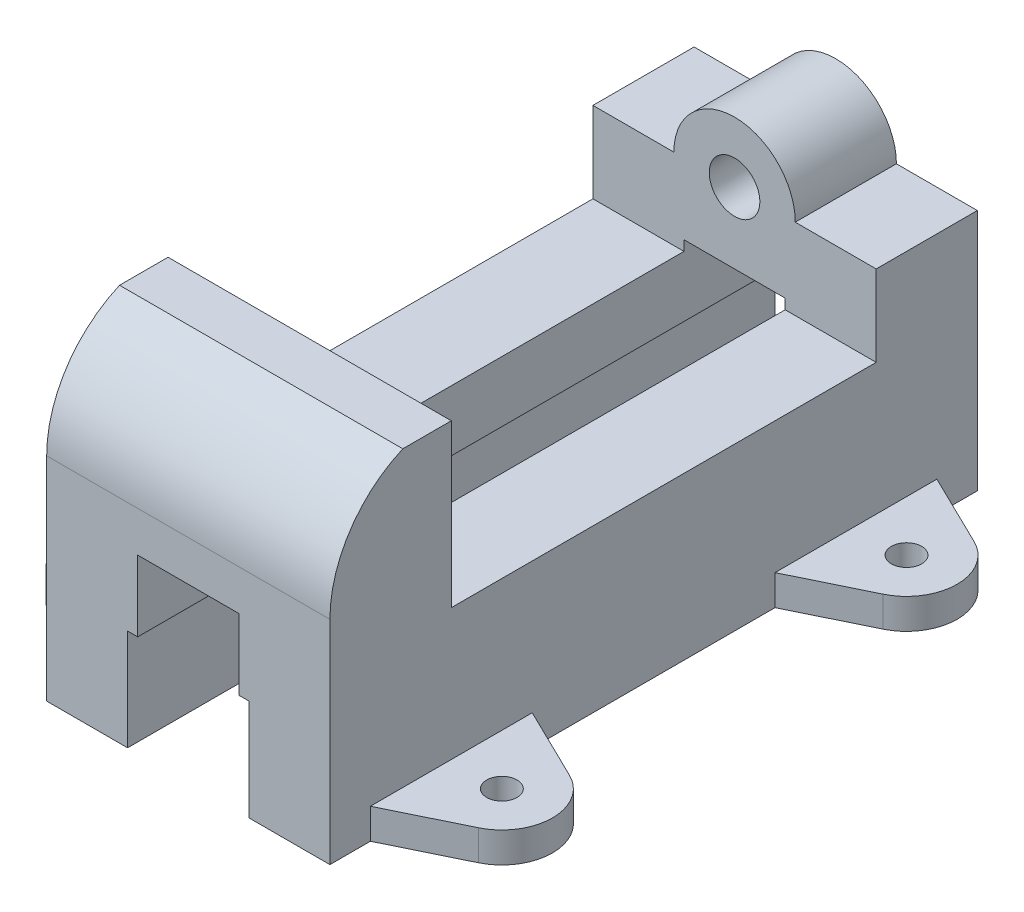
SolidWorks part; units mm, degrees
material "Gray Cast Iron"
ref_plane "Front Plane" through (0, 0, 0) normal (0, 0, 1) x (1, 0, 0)
ref_plane "Top Plane" through (0, 0, 0) normal (0, 1, 0) x (1, 0, 0)
ref_plane "Right Plane" through (0, 0, 0) normal (1, 0, 0) x (0, 0, -1)
sketch "Sketch2" plane through (0, 0, 0) normal (1, 0, 0) x (0, 0, -1)
  line L0 (0, 0) -> (0, 66.675)
  line L1 (38.1, 50.8) -> (171.45, 50.8)
  line L2 (38.1, 66.675) -> (38.1, 0) construction
  line L3 (0, 0) -> (38.1, 0)
  line L4 (38.1, 0) -> (171.45, 0)
  line L5 (171.45, 0) -> (203.2, 0)
  line L6 (203.2, 0) -> (203.2, 76.2)
  line L7 (203.2, 76.2) -> (171.45, 76.2)
  line L8 (171.45, 76.2) -> (171.45, 50.8)
  line L10 (38.1, 50.8) -> (38.1, 101.6)
  line L12 (38.1, 101.6) -> (22.8732, 101.6)
  arc A1 (22.8732, 101.6) -> (0, 66.675) centre (38.1, 66.675) ccw
  dimension "D1" = 66.675
  dimension "D2" = 38.1
  dimension "D3" = 133.35
  dimension "D4" = 31.75
  dimension "D5" = 76.2
  dimension "D6" = 31.75
  dimension "D7" = 50.8
  dimension "D8" = 50.8
extrude "Boss-Extrude1" add sketch "Sketch2" along normal blind 88.9
sketch "Sketch3" plane through (0, 0, -203.2) normal (0, 0, -1) x (-1, 0, 0)
  line L0 (-88.9, 0) -> (0, 0) construction
  line L1 (-44.45, 0) -> (-25.4, 0)
  line L2 (-44.45, 0) -> (-63.5, 0)
  line L3 (-63.5, 0) -> (-63.5, 31.75)
  line L4 (-63.5, 31.75) -> (-60.325, 31.75)
  line L5 (-60.325, 31.75) -> (-60.325, 53.975)
  line L6 (-60.325, 53.975) -> (-28.575, 53.975)
  line L7 (-28.575, 53.975) -> (-28.575, 31.75)
  line L8 (-28.575, 31.75) -> (-25.4, 31.75)
  line L9 (-25.4, 31.75) -> (-25.4, 0)
  dimension "D1" = 19.05
  dimension "D2" = 19.05
  dimension "D3" = 53.975
  dimension "D4" = 3.175
  dimension "D6" = 31.75
  dimension "D7" = 31.75
extrude "Cut-Extrude1" cut sketch "Sketch3" against normal blind 203.2
sketch "Sketch4" plane through (0, 0, -203.2) normal (0, 0, -1) x (-1, 0, 0)
  line L0 (-88.9, 76.2) -> (0, 76.2) construction
  line L1 (-63.5, 76.2) -> (-25.4, 76.2)
  arc A0 (-25.4, 76.2) -> (-63.5, 76.2) centre (-44.45, 76.2) ccw
  dimension "D1" = 38.1
extrude "Boss-Extrude2" add sketch "Sketch4" against normal blind 31.75
sketch "Sketch5" plane through (0, 0, -203.2) normal (0, 0, -1) x (-1, 0, 0)
  circle A0 centre (-44.45, 76.2) radius 7.9375
  point P0 (-44.45, 76.2)
  dimension "D3" = 15.875
  dimension "D1" = 76.2
  dimension "D2" = 44.45
extrude "Cut-Extrude2" cut sketch "Sketch5" against normal blind 31.75
sketch "Sketch6" plane through (0, 0, 0) normal (0, 1, 0) x (1, 0, 0)
  line L0 (88.9, 0) -> (88.9, 203.2) construction
  line L1 (88.9, 12.7) -> (111.7315, 23.8303)
  line L2 (88.9, 63.5) -> (111.7315, 52.3697)
  line L3 (88.9, 12.7) -> (88.9, 63.5)
  line L4 (88.9, 139.7) -> (111.7315, 150.8303)
  line L5 (88.9, 190.5) -> (111.7315, 179.3697)
  line L6 (88.9, 139.7) -> (88.9, 190.5)
  line L7 (88.9, 203.2) -> (0, 203.2)
  line L8 (88.9, 0) -> (0, 0)
  line L9 (44.45, 0) -> (44.45, 203.2)
  line L10 (0, 139.7) -> (0, 190.5)
  line L11 (0, 190.5) -> (-22.8315, 179.3697)
  line L12 (0, 139.7) -> (-22.8315, 150.8303)
  line L13 (0, 12.7) -> (-22.8315, 23.8303)
  line L14 (0, 12.7) -> (0, 63.5)
  line L15 (0, 63.5) -> (-22.8315, 52.3697)
  circle A0 centre (104.775, 38.1) radius 4.7625
  circle A1 centre (104.775, 165.1) radius 4.7625
  arc A2 (111.7315, 23.8303) -> (111.7315, 52.3697) centre (104.775, 38.1) ccw
  arc A3 (111.7315, 150.8303) -> (111.7315, 179.3697) centre (104.775, 165.1) ccw
  circle A4 centre (-15.875, 165.1) radius 4.7625
  arc A5 (-22.8315, 150.8303) -> (-22.8315, 179.3697) centre (-15.875, 165.1) cw
  arc A6 (-22.8315, 23.8303) -> (-22.8315, 52.3697) centre (-15.875, 38.1) cw
  circle A7 centre (-15.875, 38.1) radius 4.7625
  point P0 (88.9, 12.7)
  point P1 (88.9, 63.5)
  point P5 (88.9, 190.5)
  point P6 (88.9, 139.7)
  point P7 (104.775, 38.1)
  point P9 (104.775, 165.1)
  dimension "D9" = 9.525
  dimension "D10" = 31.75
  dimension "D11" = 9.525
  dimension "D12" = 31.75
  dimension "D1" = 12.7
  dimension "D2" = 50.8
  dimension "D3" = 12.7
  dimension "D4" = 50.8
  dimension "D5" = 15.875
  dimension "D6" = 15.875
  dimension "D7" = 25.4
  dimension "D8" = 25.4
extrude "Boss-Extrude3" add sketch "Sketch6" along normal blind 9.525 contours A6 L13 L14 L15 A7 | A5 L12 L10 L11 A4 | L4 A3 L5 L6 A1 | L1 A2 L2 L3 A0
